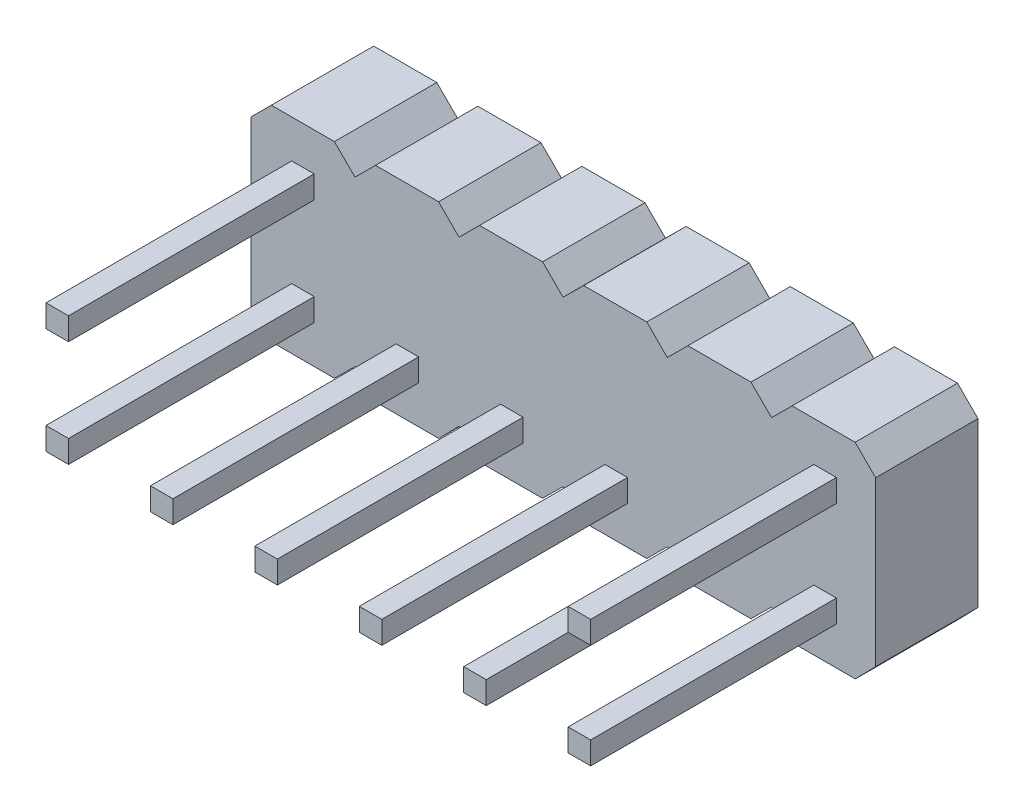
SolidWorks part; units mm, degrees
ref_plane "Front Plane" through (0, 0, 0) normal (0, 0, 1) x (1, 0, 0)
ref_plane "Top Plane" through (0, 0, 0) normal (0, 1, 0) x (1, 0, 0)
ref_plane "Right Plane" through (0, 0, 0) normal (1, 0, 0) x (0, 0, -1)
sketch "Sketch1" plane through (0, 0, 0) normal (0, 0, 1) x (1, 0, 0)
  line L0 (0, 0) -> (0, 4)
  line L1 (0, 4) -> (0.502, 4.502)
  line L2 (0.502, 4.502) -> (2.042, 4.502)
  line L3 (2.042, 4.502) -> (2.5461, 4.002)
  line L4 (2.5461, 4.002) -> (3.0461, 4.502)
  line L5 (3.0461, 4.502) -> (4.5861, 4.502)
  line L6 (0, 0) -> (0.502, -0.502)
  line L7 (0.502, -0.502) -> (2.042, -0.502)
  line L8 (2.042, -0.502) -> (2.5461, -0.002)
  line L9 (2.5461, -0.002) -> (3.0502, -0.502)
  line L10 (3.0502, -0.502) -> (4.5902, -0.502)
  line L11 (4.5861, 4.502) -> (5.0861, 4.002)
  line L12 (4.5902, -0.502) -> (5.0861, 0.0061)
  line L13 (5.0861, 4.002) -> (5.0861, 0.0061) construction
  line L14 (5.582, -0.502) -> (5.0861, 0.0061)
  line L15 (5.5861, 4.502) -> (5.0861, 4.002)
  line L16 (7.122, -0.502) -> (5.582, -0.502)
  line L17 (7.6261, -0.002) -> (7.122, -0.502)
  line L18 (8.1302, -0.502) -> (7.6261, -0.002)
  line L19 (9.6702, -0.502) -> (8.1302, -0.502)
  line L20 (10.1723, 0) -> (9.6702, -0.502)
  line L21 (7.1261, 4.502) -> (5.5861, 4.502)
  line L22 (7.6261, 4.002) -> (7.1261, 4.502)
  line L23 (8.1302, 4.502) -> (7.6261, 4.002)
  line L24 (9.6702, 4.502) -> (8.1302, 4.502)
  line L25 (10.1723, 4) -> (9.6702, 4.502)
  line L26 (10.1723, 4) -> (10.1723, 0) construction
  line L31 (10.1723, 4) -> (10.6743, 4.502)
  line L32 (10.6743, 4.502) -> (12.2143, 4.502)
  line L33 (12.2143, 4.502) -> (12.7184, 4.002)
  line L34 (12.7184, 4.002) -> (13.2184, 4.502)
  line L35 (13.2184, 4.502) -> (14.7584, 4.502)
  line L36 (10.1723, 0) -> (10.6743, -0.502)
  line L37 (10.6743, -0.502) -> (12.2143, -0.502)
  line L38 (12.2143, -0.502) -> (12.7184, -0.002)
  line L39 (12.7184, -0.002) -> (13.2225, -0.502)
  line L40 (13.2225, -0.502) -> (14.7625, -0.502)
  line L41 (14.7584, 4.502) -> (15.2584, 4.002)
  line L42 (14.7625, -0.502) -> (15.2584, 0.0061)
  line L52 (15.2584, 4.002) -> (15.2584, 0.0061)
  dimension "D1" = 4
  dimension "D2" = 0.71
  dimension "D3" = 1.54
  dimension "D4" = 0.71
  dimension "D5" = 0.5
  dimension "D6" = 0.5
  dimension "D7" = 1.54
  dimension "D8" = 1.54
  dimension "D9" = 1.54
  dimension "D10" = 0.71
  dimension "D11" = 0.71
  dimension "D12" = 0.5
  dimension "D13" = 0.71
  dimension "D14" = 0.5
  dimension "D15" = 0.71
extrude "Boss-Extrude1" add sketch "Sketch1" along normal blind 2.5
sketch "Sketch2" plane through (0, 0, 2.5) normal (0, 0, 1) x (1, 0, 0)
  line L0 (0.502, -0.502) -> (2.042, -0.502) construction
  line L1 (1, 0.428) -> (1.55, 0.428)
  line L2 (1, 0.428) -> (1, 0.978)
  line L3 (1, 0.978) -> (1.55, 0.978)
  line L4 (1.55, 0.428) -> (1.55, 0.978)
  line L5 (1, 0.428) -> (1.55, 0.978) construction
  line L6 (1, 0.978) -> (1.55, 0.428) construction
  line L7 (0, 4) -> (0, 0) construction
  line L8 (0, 2) -> (2.4813, 2) construction
  line L9 (1, 3.022) -> (1.55, 3.022)
  line L10 (1.55, 3.572) -> (1.55, 3.022)
  line L11 (1, 3.572) -> (1.55, 3.572)
  line L12 (1, 3.572) -> (1, 3.022)
  line L14 (3.55, 0.428) -> (3.55, 0.978)
  line L15 (3.55, 0.428) -> (4.1, 0.428)
  line L16 (4.1, 0.428) -> (4.1, 0.978)
  line L17 (3.55, 0.978) -> (4.1, 0.978)
  line L18 (6.1, 0.428) -> (6.1, 0.978)
  line L19 (6.1, 0.428) -> (6.65, 0.428)
  line L20 (6.65, 0.428) -> (6.65, 0.978)
  line L21 (6.1, 0.978) -> (6.65, 0.978)
  line L22 (8.65, 0.428) -> (8.65, 0.978)
  line L23 (8.65, 0.428) -> (9.2, 0.428)
  line L24 (9.2, 0.428) -> (9.2, 0.978)
  line L25 (8.65, 0.978) -> (9.2, 0.978)
  line L26 (11.2, 0.428) -> (11.2, 0.978)
  line L27 (11.2, 0.428) -> (11.75, 0.428)
  line L28 (11.75, 0.428) -> (11.75, 0.978)
  line L29 (11.2, 0.978) -> (11.75, 0.978)
  line L30 (13.75, 0.428) -> (13.75, 0.978)
  line L31 (13.75, 0.428) -> (14.3, 0.428)
  line L32 (14.3, 0.428) -> (14.3, 0.978)
  line L33 (13.75, 0.978) -> (14.3, 0.978)
  line L34 (13.75, 2.978) -> (13.75, 3.528)
  line L35 (13.75, 3.528) -> (14.3, 3.528)
  line L36 (14.3, 2.978) -> (14.3, 3.528)
  line L37 (13.75, 2.978) -> (14.3, 2.978)
  point P0 (1.275, 0.703)
  point P7 (1.272, -0.502)
  dimension "D1" = 0.55
  dimension "D2" = 0.55
  dimension "D3" = 0.93
  dimension "D4" = 1
  dimension "D6" = 2
  dimension "D5" = 6
extrude "Boss-Extrude2" add sketch "Sketch2" along normal blind 6
